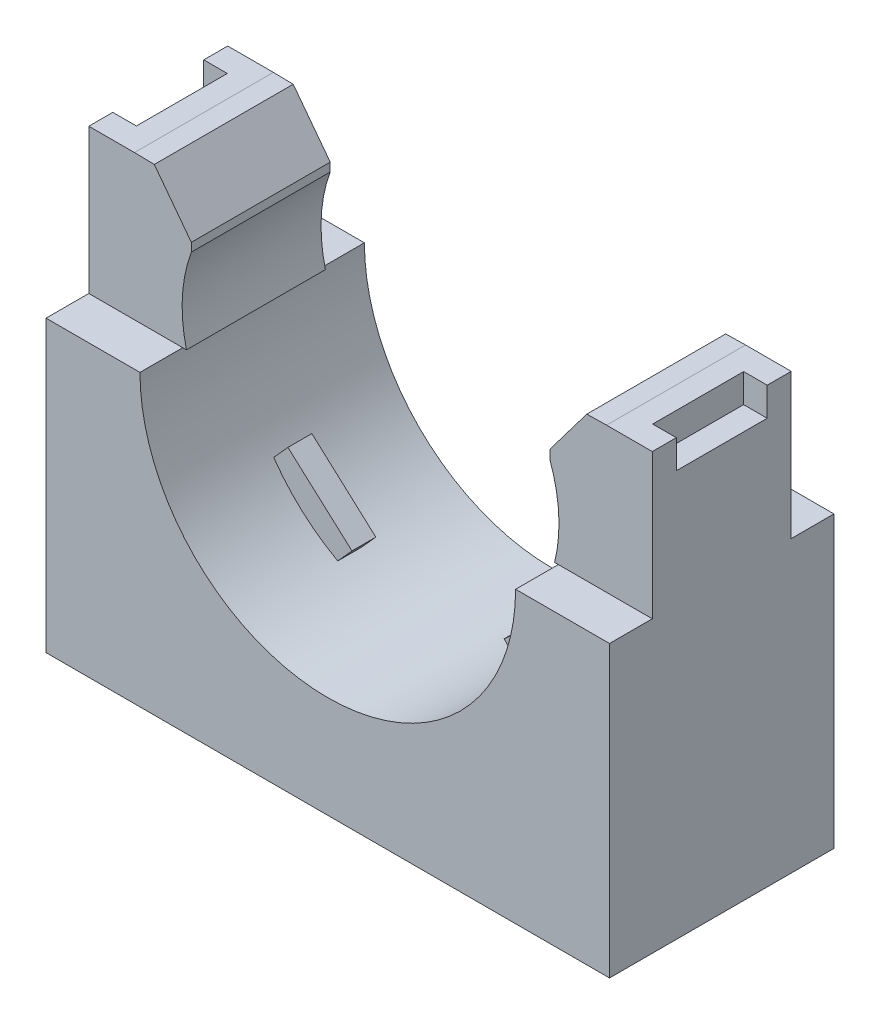
SolidWorks part; units mm, degrees
ref_plane "Front Plane" through (0, 0, 0) normal (0, 0, 1) x (1, 0, 0)
ref_plane "Top Plane" through (0, 0, 0) normal (0, 1, 0) x (1, 0, 0)
ref_plane "Right Plane" through (0, 0, 0) normal (1, 0, 0) x (0, 0, -1)
sketch "Sketch1" plane through (0, 0, 0) normal (0, 0, 1) x (1, 0, 0)
  line L0 (-14.986, -11.557) -> (14.986, 11.557) construction
  line L1 (-14.986, 11.557) -> (14.986, 11.557)
  line L2 (-14.986, 11.557) -> (-14.986, -11.557)
  line L3 (-14.986, -11.557) -> (14.986, -11.557)
  line L4 (14.986, 11.557) -> (14.986, -11.557)
  arc A0 (-9.7893, 1.8564) -> (9.7927, 1.8735) centre (0, 3.8523) ccw construction
  point P4 (0, 0)
  dimension "D3" = 15.4093
  dimension "D4" = 9.9907
  dimension "B" = 29.972
  dimension "C" = 23.114
extrude "Extrude1" add sketch "Sketch1" along normal blind 11.938
sketch "Sketch2" plane through (0, 0, 11.938) normal (0, 0, 1) x (1, 0, 0)
  line L1 (-9.9907, 3.8523) -> (-9.7909, 3.8523)
  line L2 (9.7909, 3.8523) -> (9.9907, 3.8523)
  line L3 (9.5329, 8.4799) -> (9.5329, 11.5041)
  line L4 (9.5329, 11.5041) -> (12.5571, 11.557)
  line L5 (14.986, 11.557) -> (-14.986, 11.557) construction
  line L6 (0, 0) -> (0, 22.8281) construction
  line L7 (-9.5329, 11.5041) -> (-12.5571, 11.557)
  line L8 (-9.5329, 8.4799) -> (-9.5329, 11.5041)
  line L9 (12.5571, 11.557) -> (-12.5571, 11.557)
  line L10 (14.986, -11.557) -> (14.986, 11.557) construction
  arc A0 (-9.9907, 3.8523) -> (9.9907, 3.8523) centre (0, 3.8523) ccw
  arc A1 (9.5329, 8.4799) -> (9.7909, 3.8523) centre (2.1566, 5.7478) cw
  arc A2 (-9.5329, 8.4799) -> (-9.7909, 3.8523) centre (-2.1566, 5.7478) ccw
  arc A3 (-9.7893, 1.8564) -> (9.7927, 1.8735) centre (0, 3.8523) ccw construction
  dimension "D1" = 0.1998
  dimension "D3" = 7.8661
  dimension "D2" = 3.0242
  dimension "D4" = 3.0242
  dimension "D7" = 5.4531
  dimension "D8" = 4.6276
extrude "Cut-Extrude1" cut sketch "Sketch2" against normal through all
sketch "Sketch3" plane through (0, 0, 0) normal (1, 0, 0) x (0, 0, -1)
  line L1 (-11.938, 3.8523) -> (-9.6634, 3.8523)
  line L2 (-9.6634, 11.557) -> (-9.6634, 3.8523)
  line L3 (-11.938, 3.8523) -> (-11.938, 11.557)
  line L4 (-2.2746, 11.557) -> (-2.2746, 3.8523)
  line L5 (-5.969, 31.6865) -> (-5.969, 10.4775) construction
  line L6 (-11.938, 11.557) -> (0, 11.557) construction
  line L7 (-11.938, -11.557) -> (-11.938, 11.557) construction
  line L8 (-11.938, 11.557) -> (-9.6634, 11.557)
  line L9 (0, 3.8523) -> (0, 11.557)
  line L10 (0, 3.8523) -> (-2.2746, 3.8523)
  line L11 (-2.2746, 11.557) -> (0, 11.557)
  line L13 (0, -11.557) -> (0, 11.557) construction
  dimension "D2" = 2.2746
extrude "Cut-Extrude2" cut sketch "Sketch3" against normal through all and the other way through all
sketch "Sketch4" plane through (0, -11.557, 0) normal (0, -1, 0) x (1, 0, 0)
  line L12 (-14.986, 11.1442) -> (14.986, 11.1442)
  line L13 (-14.1922, 11.1442) -> (14.1923, 11.1442)
  line L14 (-14.1922, 0.7937) -> (-14.1922, 11.938)
  line L15 (14.1923, 0.7937) -> (-14.1922, 0.7937)
  line L16 (14.1923, 11.938) -> (14.1923, 0.7937)
  line L17 (-14.1922, 0.7937) -> (-14.1922, 11.1442)
  line L18 (14.1923, 0.7937) -> (-14.1922, 0.7937)
  line L19 (14.1923, 11.1442) -> (14.1923, 0.7937)
  dimension "D1" = 0.7937
  dimension "D2" = 0.7937
extrude "Cut-Extrude3" cut sketch "Sketch4" against normal blind 0.254
sketch "Sketch5" plane through (0, 11.557, 0) normal (0, 1, 0) x (1, 0, 0)
  line L0 (-14.986, -2.2746) -> (-12.5571, -2.2746) construction
  line L2 (-14.986, -3.5503) -> (-13.7309, -3.5503)
  line L3 (-14.986, -3.5503) -> (-14.986, -8.3877)
  line L4 (-14.986, -8.3877) -> (-13.7309, -8.3877)
  line L6 (-13.7309, -3.5503) -> (-13.7309, -8.3877)
  line L10 (14.986, -3.5503) -> (13.7309, -3.5503)
  line L11 (14.986, -3.5503) -> (14.986, -8.3877)
  line L12 (14.986, -8.3877) -> (13.7309, -8.3877)
  line L13 (13.7309, -3.5503) -> (13.7309, -8.3877)
  line L14 (14.986, -9.6634) -> (14.986, -2.2746) construction
  line L15 (-14.986, -9.6634) -> (-14.986, -2.2746) construction
  line L16 (12.5571, -5.969) -> (-12.5571, -5.969) construction
  line L17 (12.5571, -2.2746) -> (12.5571, -9.6634) construction
  line L18 (-12.5571, -2.2746) -> (-12.5571, -9.6634) construction
  dimension "D1" = 1.2757
  dimension "D2" = 1.1737
extrude "Cut-Extrude4" cut sketch "Sketch5" against normal blind 1.524
ref_plane "Plane1" through (0, 0, 5.969) normal (0, 0, -1) x (-1, 0, 0)
sketch "Sketch6" plane through (0, 0, 5.969) normal (0, 0, -1) x (-1, 0, 0)
  line L0 (0, 0) -> (0, -34.0604) construction
  line L1 (2.54, -11.303) -> (0, -11.303)
  line L2 (14.1922, -11.303) -> (-14.1923, -11.303) construction
  line L3 (0, -6.223) -> (4.953, -6.223)
  line L4 (4.953, -6.223) -> (4.953, -8.763)
  line L5 (4.953, -8.763) -> (2.54, -8.763)
  line L6 (2.54, -8.763) -> (2.54, -11.303)
  line L7 (0, -11.303) -> (0, -6.223)
  dimension "E" = 9.906
  dimension "D" = 5.08
  dimension "D3" = 2.54
  dimension "D4" = 5.08
revolve "Cut-Revolve1" cut sketch "Sketch6" angle 360 about L0
sketch "Sketch7" plane through (0, 0, 5.969) normal (0, 0, -1) x (-1, 0, 0)
  line L0 (0, 16.5622) -> (0, -24.4387) construction
  line L1 (0, 3.8523) -> (5.7503, -2.534) construction
  line L2 (4.0476, -4.0672) -> (7.4531, -1.0009)
  line L3 (7.4531, -1.0009) -> (8.2096, -1.8411)
  line L4 (4.0476, -4.0672) -> (4.8041, -4.9075)
  line L5 (-4.0476, -4.0672) -> (-4.8041, -4.9075)
  line L6 (-7.4531, -1.0009) -> (-8.2096, -1.8411)
  line L7 (-4.0476, -4.0672) -> (-7.4531, -1.0009)
  arc A0 (-9.7927, 1.8735) -> (9.7893, 1.8564) centre (0, 3.8523) ccw construction
  arc A3 (4.8041, -4.9075) -> (8.2096, -1.8411) centre (0, 3.8523) ccw
  arc A4 (-4.8041, -4.9075) -> (-8.2096, -1.8411) centre (0, 3.8523) cw
  point P9 (5.7503, -2.534)
  dimension "D1" = 42
  dimension "D2" = 4.5826
  dimension "D3" = 1.1307
extrude "Extrude2" add sketch "Sketch7" along normal mid plane 1.27
sketch "Sketch8" plane through (0, 0, 0) normal (0, 0, 1) x (1, 0, 0)
  line L0 (-9.5329, 11.5385) -> (-11.5014, 11.5385)
  line L1 (-9.5329, 11.5385) -> (-9.5329, 8.935)
  line L3 (-9.5329, 8.935) -> (-11.5014, 11.5385)
  line L4 (0, 0) -> (0, -13.7082) construction
  line L7 (9.5329, 11.5385) -> (11.5014, 11.5385)
  line L8 (9.5329, 11.5385) -> (9.5329, 8.935)
  line L9 (9.5329, 8.935) -> (11.5014, 11.5385)
  dimension "D1" = 1.9685
  dimension "D2" = 2.6035
extrude "Cut-Extrude5" cut sketch "Sketch8" along normal through all
equation "\"D3@Sketch1\" = (\"C@Sketch1\"/3)*2"
equation "\"D4@Sketch1\" = \"B@Sketch1\"/3"
equation "\"D3@Sketch2\" = ((\"D4@Sketch1\"/4)*3)+0.0146875"
equation "\"D8@Sketch2\" = (\"D3@Sketch2\"/2)+0.02734375"
equation "\"D4@Sketch2\" = ((\"D8@Sketch2\"/4)*3)-0.009765625-0.0078125"
equation "\"D7@Sketch2\" = (\"D4@Sketch2\"*2)-0.0234375"
equation "\"D2@Sketch7\" = (\"D4@Sketch1\"/2)-0.01625"
equation "\"D3@Sketch7\" = \"D2@Sketch7\"/3-0.015625"
equation "\"D2@Sketch2\" = \"D4@Sketch2\""
equation "\"D1@Sketch2\" = \"D4@Sketch1\"/50"
equation "\"D4@Sketch6\" = \"D@Sketch6\""
equation "\"D3@Sketch6\" = \"D4@Sketch6\"/2"
